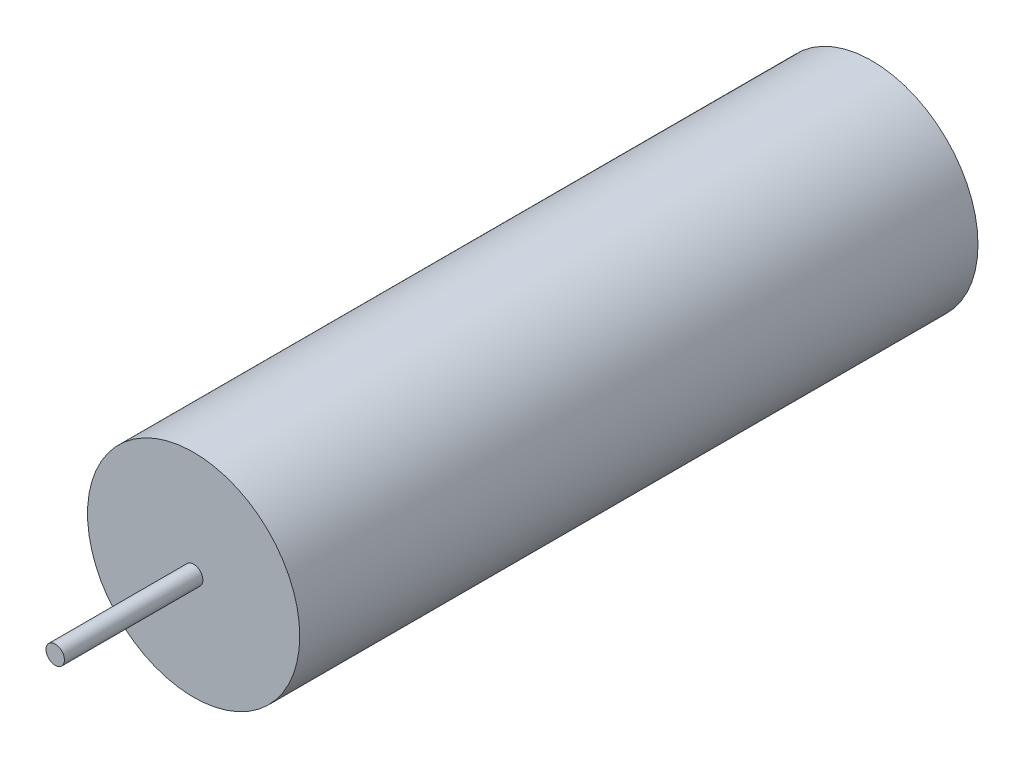
SolidWorks part; units mm, degrees
ref_plane "Front Plane" through (0, 0, 0) normal (0, 0, 1) x (1, 0, 0)
ref_plane "Top Plane" through (0, 0, 0) normal (0, 1, 0) x (1, 0, 0)
ref_plane "Right Plane" through (0, 0, 0) normal (1, 0, 0) x (0, 0, -1)
sketch "Sketch1" plane through (0, 0, 0) normal (0, 0, 1) x (1, 0, 0)
  circle A0 centre (0, 0) radius 2.921
  dimension "D1" = 5.842
extrude "Boss-Extrude1" add sketch "Sketch1" along normal blind 18.669
sketch "Sketch2" plane through (0, 0, 18.669) normal (0, 0, 1) x (1, 0, 0)
  circle A0 centre (0, 0) radius 0.254
  dimension "D1" = 0.508
extrude "Boss-Extrude2" add sketch "Sketch2" along normal blind 3.81
